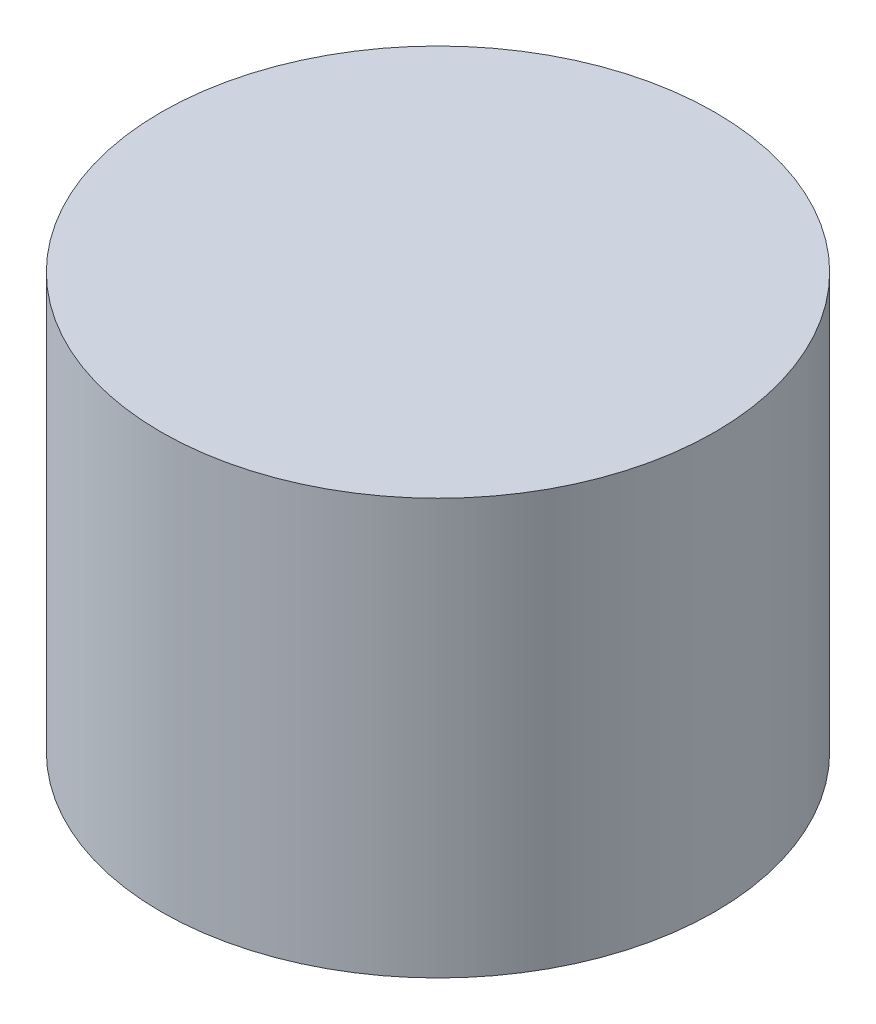
SolidWorks part; units mm, degrees
material "ABS"
ref_plane "Front Plane" through (0, 0, 0) normal (0, 0, 1) x (1, 0, 0)
ref_plane "Top Plane" through (0, 0, 0) normal (0, 1, 0) x (1, 0, 0)
ref_plane "Right Plane" through (0, 0, 0) normal (1, 0, 0) x (0, 0, -1)
sketch "Sketch2" plane through (0, 0, 0) normal (0, 1, 0) x (1, 0, 0)
  circle A0 centre (0, 0) radius 25.4
  dimension "D1" = 50.8
extrude "Boss-Extrude1" add sketch "Sketch2" along normal blind 38.1
